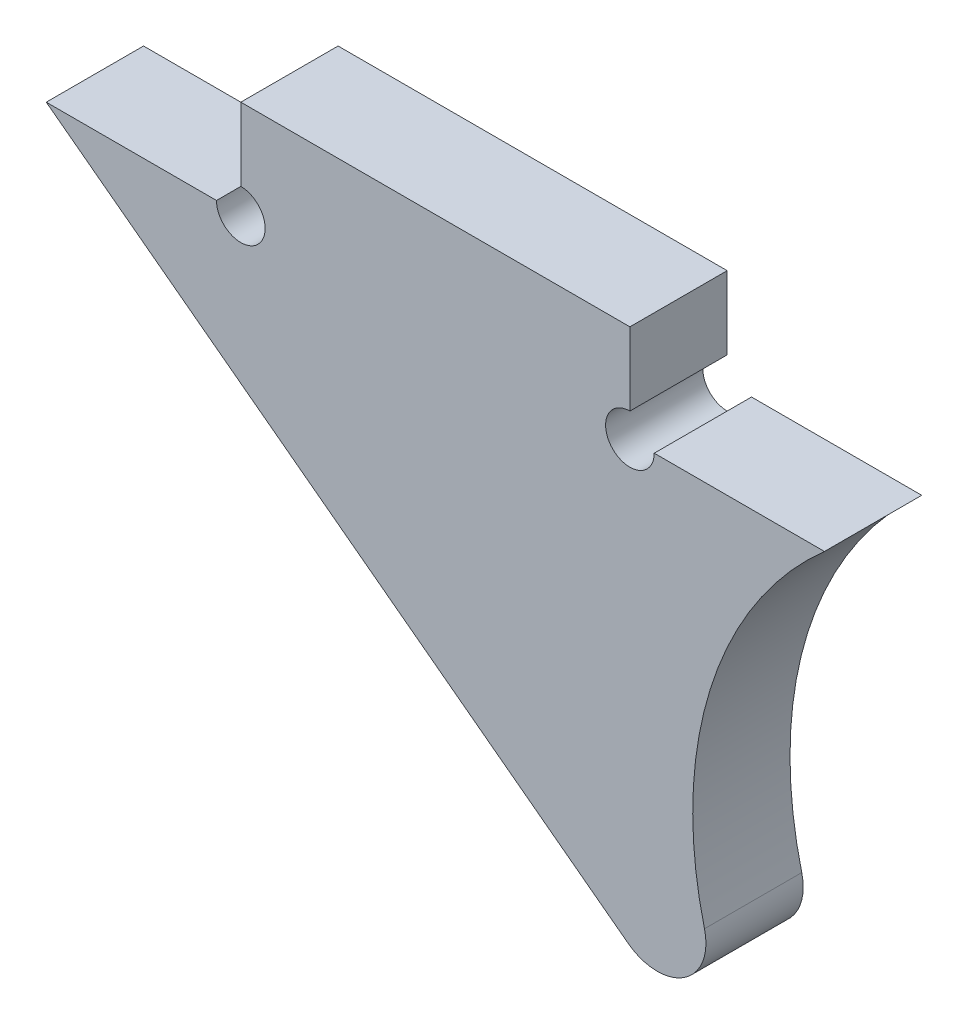
SolidWorks part; units mm, degrees
material "AISI 4340 Steel, annealed"
ref_plane "Front Plane" through (0, 0, 0) normal (0, 0, 1) x (1, 0, 0)
ref_plane "Top Plane" through (0, 0, 0) normal (0, 1, 0) x (1, 0, 0)
ref_plane "Right Plane" through (0, 0, 0) normal (1, 0, 0) x (0, 0, -1)
sketch "Sketch2" plane through (0, 0, 0) normal (0, 0, 1) x (1, 0, 0)
  line L0 (-19.05, 0) -> (-25.4, 0)
  line L1 (-6.35, 0) -> (0, 0)
  line L3 (-25.4, 0) -> (0.7679, -19.6757)
  line L4 (-6.35, 3.175) -> (-19.05, 3.175)
  line L5 (-19.05, 3.175) -> (-19.05, 0)
  line L6 (-19.05, 0) -> (-6.35, 0)
  line L7 (-6.35, 0) -> (-6.35, 3.175)
  line L8 (-6.35, 3.175) -> (-19.05, 3.175)
  line L9 (-19.05, 3.175) -> (-19.05, 0)
  line L10 (-19.05, 0) -> (-6.35, 0) construction
  line L11 (-6.35, 0) -> (-6.35, 3.175)
  circle A0 centre (8.4003, -9.525) radius 12.7 construction
  arc A1 (0, 0) -> (0.7679, -19.6757) centre (8.4003, -9.525) ccw
  dimension "D2" = 25.4
  dimension "D1" = 0
extrude "Boss-Extrude1" add sketch "Sketch2" along normal up to surface (3.175 mm away)
fillet "Fillet1" radius 1.5875 1 edges at (0.7679, -19.6757, 1.5875)
sketch "Sketch3" plane through (0, 0, 3.175) normal (0, 0, 1) x (1, 0, 0)
  line L0 (-19.05, 0) -> (-25.4, 0) construction
  line L1 (-19.05, 3.175) -> (-19.05, 0) construction
  line L2 (0, 0) -> (-6.35, 0) construction
  line L3 (-6.35, 0) -> (-6.35, 3.175) construction
  line L4 (-19.05, 0) -> (-25.4, 0) construction
  line L5 (-19.05, 3.175) -> (-19.05, 0) construction
  line L6 (0, 0) -> (-6.35, 0) construction
  line L7 (-6.35, 0) -> (-6.35, 3.175) construction
  circle A0 centre (-19.05, 0) radius 0.7937
  circle A1 centre (-6.35, 0) radius 0.7938
  dimension "D1" = 1.5875
extrude "Cut-Extrude1" cut sketch "Sketch3" against normal up to surface (3.175 mm away) up to face at (-10.964, -2.6105, 0)
